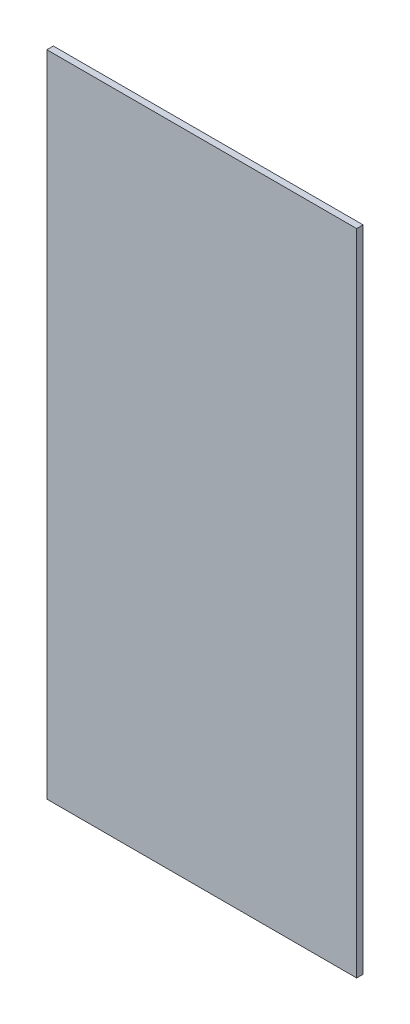
SolidWorks part; units mm, degrees
ref_plane "Front" through (0, 0, 0) normal (0, 0, 1) x (1, 0, 0)
ref_plane "Top" through (0, 0, 0) normal (0, 1, 0) x (1, 0, 0)
ref_plane "Right" through (0, 0, 0) normal (1, 0, 0) x (0, 0, -1)
sketch "Sketch2" plane through (0, 0, 0) normal (0, 0, 1) x (1, 0, 0)
  line L1 (0, 0) -> (152.4, 0)
  line L2 (0, 0) -> (0, 319.278)
  line L3 (0, 319.278) -> (152.4, 319.278)
  line L4 (152.4, 0) -> (152.4, 319.278)
  dimension "D1" = 152.4
  dimension "D2" = 319.278
extrude "Boss-Extrude1" add sketch "Sketch2" along normal blind 3.175
sketch "Sketch4"
